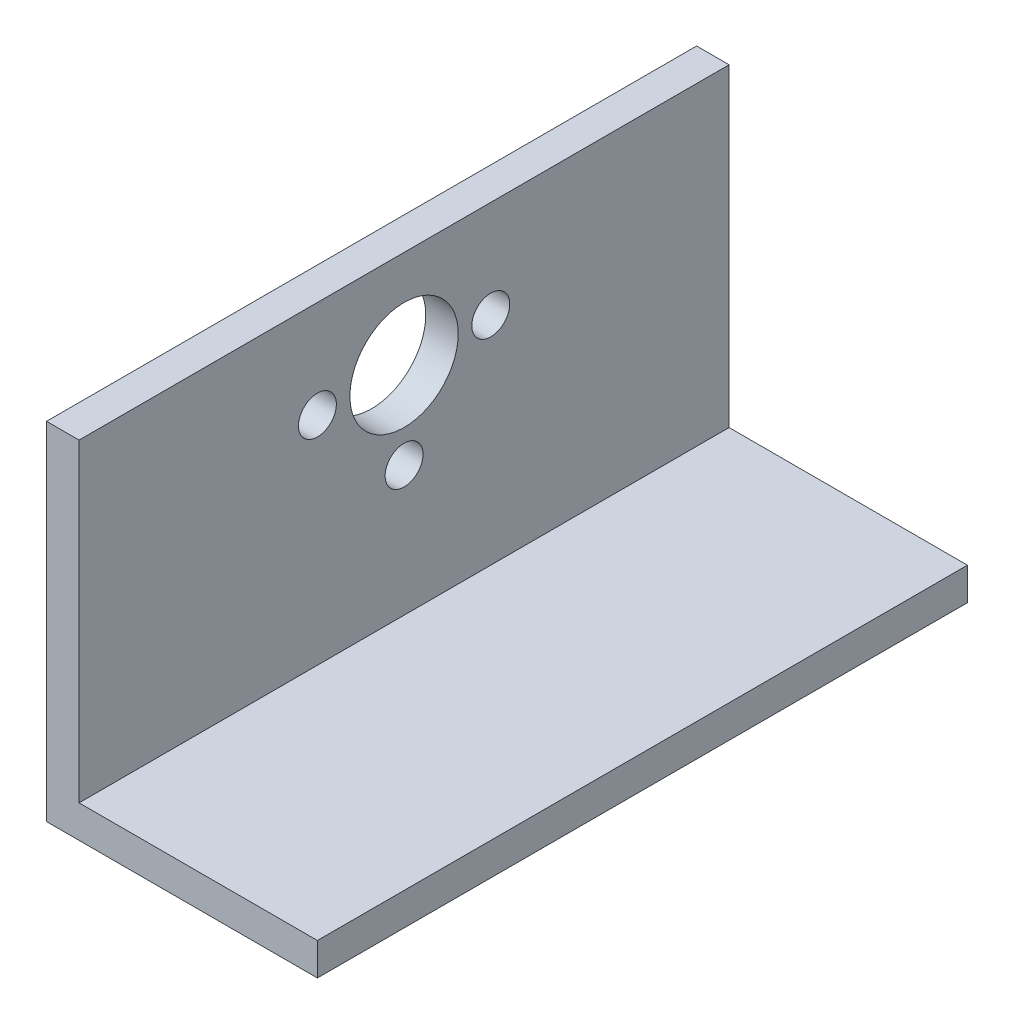
SolidWorks part; units mm, degrees
ref_plane "Front Plane" through (0, 0, 0) normal (0, 0, 1) x (1, 0, 0)
ref_plane "Top Plane" through (0, 0, 0) normal (0, 1, 0) x (1, 0, 0)
ref_plane "Right Plane" through (0, 0, 0) normal (1, 0, 0) x (0, 0, -1)
sketch "Sketch1" plane through (0, 0, 0) normal (0, 0, 1) x (1, 0, 0)
  line L0 (-7.8975, 31.3476) -> (-7.8975, 2.3476)
  line L1 (-7.8975, 2.3476) -> (14.1025, 2.3476)
  line L2 (14.1025, 2.3476) -> (14.1025, -0.6524)
  line L3 (14.1025, -0.6524) -> (-10.8975, -0.6524)
  line L4 (-10.8975, -0.6524) -> (-10.8975, 31.3476)
  line L5 (-10.8975, 31.3476) -> (-7.8975, 31.3476)
  dimension "D1" = 3
  dimension "D2" = 3
  dimension "D3" = 32
  dimension "D4" = 25
extrude "Boss-Extrude1" add sketch "Sketch1" along normal blind 60
hole_wizard "Hole for M5 300® SC Nuts (SP)1" positions "Sketch2" profile "Sketch3" hole size "M5x0.8" standard "PEM® Metric" end condition through all
sketch "Sketch2" plane through (-7.8975, 0, 0) normal (1, 0, 0) x (0, 0, -1)
  line L0 (-60, -0.6524) -> (0, -0.6524) construction
  line L1 (0, 2.3476) -> (0, 31.3476) construction
  point P0 (-30, 22.3476)
  dimension "D1" = 23
  dimension "D2" = 30
sketch "Sketch3" plane through (-7.8975, 22.3476, 30) normal (0, 1, 0) x (0, 0, -1)
  line L0 (0, 0) -> (0, 3)
  line L1 (0, 3) -> (5, 3)
  line L2 (5, 3) -> (5, 0)
  line L5 (5, 0) -> (0, 0)
  line L11 (0, -6.35) -> (0, 107.95) construction
  dimension "Thru Hole Dia." = 10
  dimension "Thru Hole Depth" = 3
hole_wizard "Hole for M5 300® SC Nuts (SP)2" positions "Sketch4" profile "Sketch5" hole size "M5x0.8" standard "PEM® Metric" end condition through all
sketch "Sketch4" plane through (-7.8975, 0, 0) normal (1, 0, 0) x (0, 0, -1)
  line L0 (-60, -0.6524) -> (0, -0.6524) construction
  line L1 (0, 2.3476) -> (0, 31.3476) construction
  circle A1 centre (-30, 22.3476) radius 5 construction
  point P0 (-22, 22.3476)
  point P2 (-38, 22.3476)
  point P4 (-30, 14.3476)
  dimension "D4" = 8
  dimension "D1" = 23
  dimension "D2" = 8
  dimension "D3" = 16
  dimension "D5" = 30
sketch "Sketch5" plane through (-7.8975, 22.3476, 22) normal (0, 1, 0) x (0, 0, -1)
  line L0 (0, 0) -> (0, 3)
  line L1 (0, 3) -> (1.75, 3)
  line L2 (1.75, 3) -> (1.75, 0)
  line L5 (1.75, 0) -> (0, 0)
  line L11 (0, -6.35) -> (0, 107.95) construction
  dimension "Thru Hole Dia." = 3.5
  dimension "Thru Hole Depth" = 3
